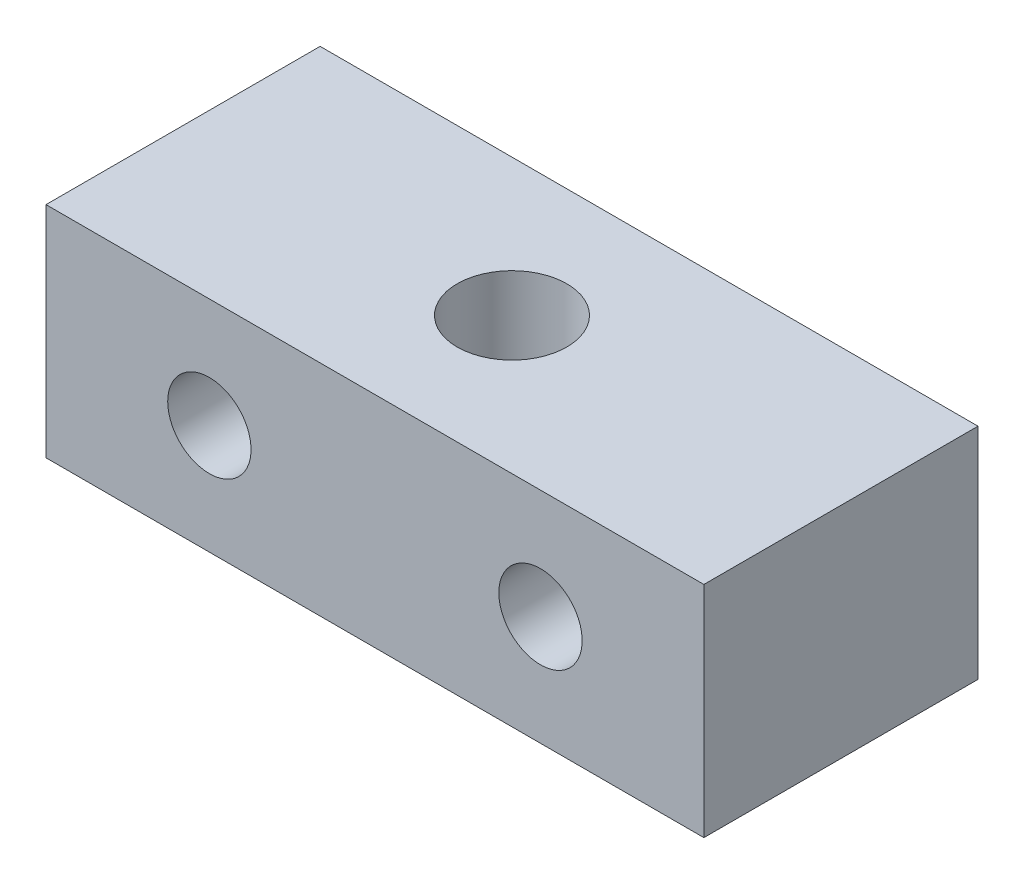
SolidWorks part; units mm, degrees
ref_plane "Front Plane" through (0, 0, 0) normal (0, 0, 1) x (1, 0, 0)
ref_plane "Top Plane" through (0, 0, 0) normal (0, 1, 0) x (1, 0, 0)
ref_plane "Right Plane" through (0, 0, 0) normal (1, 0, 0) x (0, 0, -1)
sketch "Sketch1" plane through (0, 0, 0) normal (0, 1, 0) x (1, 0, 0)
  line L1 (-19.05, 7.9375) -> (19.05, 7.9375)
  line L2 (-19.05, 7.9375) -> (-19.05, -7.9375)
  line L3 (-19.05, -7.9375) -> (19.05, -7.9375)
  line L4 (19.05, 7.9375) -> (19.05, -7.9375)
  line L5 (-19.05, 7.9375) -> (19.05, -7.9375) construction
  line L6 (-19.05, -7.9375) -> (19.05, 7.9375) construction
  point P0 (0, 0)
  dimension "D1" = 15.875
  dimension "D2" = 38.1
extrude "Boss-Extrude1" add sketch "Sketch1" along normal blind 12.7
sketch "Sketch2" plane through (0, 0, -7.9375) normal (0, 0, -1) x (-1, 0, 0)
  line L0 (0, 0) -> (0, 12.7) construction
  line L1 (-19.05, 0) -> (19.05, 0) construction
  line L2 (-19.05, 12.7) -> (19.05, 12.7) construction
  line L3 (-9.5885, 6.35) -> (9.5885, 6.35) construction
  circle A0 centre (-9.5885, 6.35) radius 2.413
  circle A1 centre (9.5885, 6.35) radius 2.413
  point P13 (0, 6.35)
  dimension "D2" = 4.826
  dimension "D3" = 19.177
extrude "Cut-Extrude1" cut sketch "Sketch2" against normal through all
sketch "Sketch3" plane through (0, 12.7, 0) normal (0, 1, 0) x (1, 0, 0)
  circle A0 centre (0, 0) radius 3.175
  dimension "D1" = 6.35
extrude "Cut-Extrude2" cut sketch "Sketch3" against normal through all
